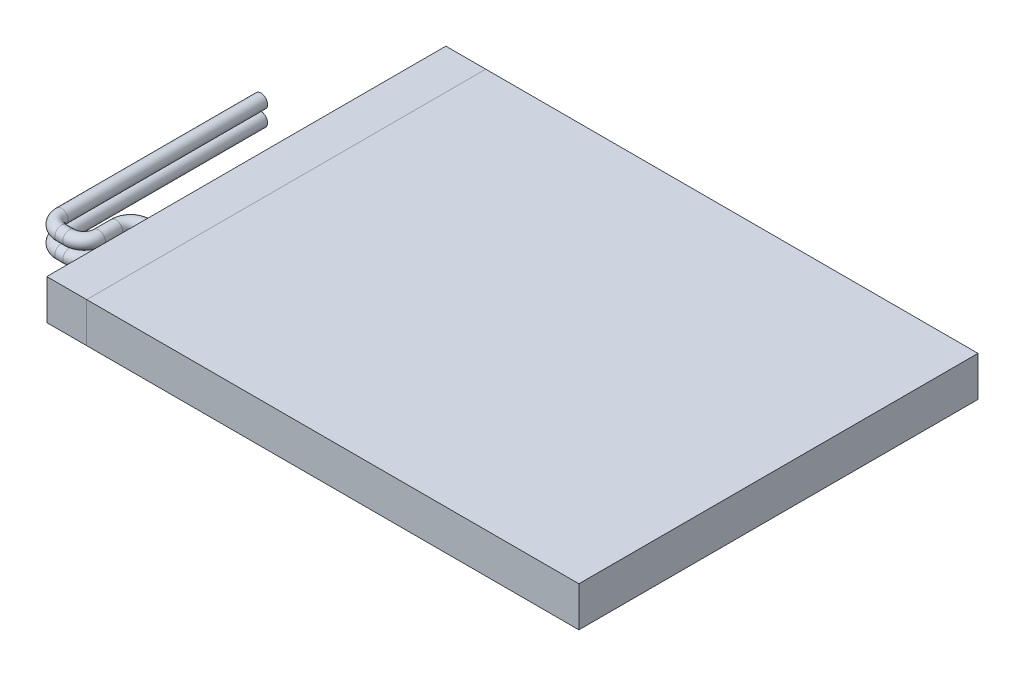
SolidWorks part; units mm, degrees
ref_plane "Front Plane" through (0, 0, 0) normal (0, 0, 1) x (1, 0, 0)
ref_plane "Top Plane" through (0, 0, 0) normal (0, 1, 0) x (1, 0, 0)
ref_plane "Right Plane" through (0, 0, 0) normal (1, 0, 0) x (0, 0, -1)
sketch "Sketch1" plane through (0, 0, 0) normal (0, 1, 0) x (1, 0, 0)
  line L1 (-20, 15) -> (20, 15)
  line L2 (-20, 15) -> (-20, -15)
  line L3 (-20, -15) -> (20, -15)
  line L4 (20, 15) -> (20, -15)
  dimension "D1" = 40
  dimension "D2" = 30
  dimension "D3" = 15
  dimension "D4" = 20
extrude "Boss-Extrude1" add sketch "Sketch1" along normal blind 3
sketch "Sketch2" plane through (0, 3, 0) normal (0, 1, 0) x (1, 0, 0)
  line L0 (-20, -15) -> (20, -15) construction
  line L1 (-20, 15) -> (-17, 15)
  line L2 (-20, 15) -> (-20, -15)
  line L3 (-20, -15) -> (-17, -15)
  line L4 (-17, 15) -> (-17, -15)
  dimension "D1" = 3
ref_plane "Plane1" through (0, 1.2, 0) normal (0, -1, 0) x (-1, 0, 0)
sketch "Sketch3" plane through (0, 1.2, 0) normal (0, -1, 0) x (-1, 0, 0)
  line L0 (20, -7.5) -> (20.1, -7.5)
  line L2 (21.2, -8.6) -> (21.2, -9.9)
  line L3 (22.3, -11) -> (22.9, -11)
  line L4 (24, -9.9) -> (24, 5.1)
  line L6 (20, 15) -> (20, -15) construction
  line L7 (20, -15) -> (-20, -15) construction
  arc A0 (21.2, -8.6) -> (20.1, -7.5) centre (20.1, -8.6) ccw
  arc A1 (24, -9.9) -> (22.9, -11) centre (22.9, -9.9) cw
  arc A2 (22.3, -11) -> (21.2, -9.9) centre (22.3, -9.9) cw
  point P11 (21.2, -7.5)
  point P16 (21.2, -11)
  dimension "D5" = 1.1
  dimension "D6" = 1.1
  dimension "D1" = 4
  dimension "D2" = 1.2
  dimension "D3" = 7.5
  dimension "D4" = 3.5
  dimension "D7" = 15
ref_plane "Plane2" through (0, 2.4, 0) normal (0, -1, 0) x (-1, 0, 0)
sketch "Sketch4" plane through (0, 2.4, 0) normal (0, -1, 0) x (-1, 0, 0)
  line L0 (20, -7.5) -> (20.1, -7.5) construction
  line L1 (21.2, -8.6) -> (21.2, -9.9) construction
  line L2 (22.3, -11) -> (22.9, -11) construction
  line L3 (24, -9.9) -> (24, 5.1) construction
  line L4 (20, -7.5) -> (20.1, -7.5)
  line L5 (21.2, -8.6) -> (21.2, -9.9)
  line L6 (22.3, -11) -> (22.9, -11)
  line L7 (24, -9.9) -> (24, 5.1)
  arc A0 (21.2, -8.6) -> (20.1, -7.5) centre (20.1, -8.6) ccw construction
  arc A1 (21.2, -9.9) -> (22.3, -11) centre (22.3, -9.9) ccw construction
  arc A2 (22.9, -11) -> (24, -9.9) centre (22.9, -9.9) ccw construction
  arc A3 (21.2, -8.6) -> (20.1, -7.5) centre (20.1, -8.6) ccw
  arc A4 (21.2, -9.9) -> (22.3, -11) centre (22.3, -9.9) ccw
  arc A5 (22.9, -11) -> (24, -9.9) centre (22.9, -9.9) ccw
sketch "Sketch5" plane through (-20, 0, 0) normal (-1, 0, 0) x (0, 0, 1)
  line L0 (7.5, 2.4) -> (8.6, 2.4) construction
  line L1 (9.9, 2.4) -> (-5.1, 2.4) construction
  line L2 (15, 3) -> (15, 0) construction
  circle A0 centre (7.5, 2.4) radius 0.5
  dimension "D1" = 1
  dimension "D2" = 7.5
sketch "Sketch7" plane through (-20, 0, 0) normal (-1, 0, 0) x (0, 0, 1)
  circle A0 centre (7.5, 1.2) radius 0.5
  dimension "D1" = 1
sweep "Sweep1" add profiles "Sketch7" path "Sketch3"
sweep "Sweep2" add profiles "Sketch5" path "Sketch4"
split "Split1" trim tools "Sketch2" bodies to split 104 resulting bodies 106 107 108 109
